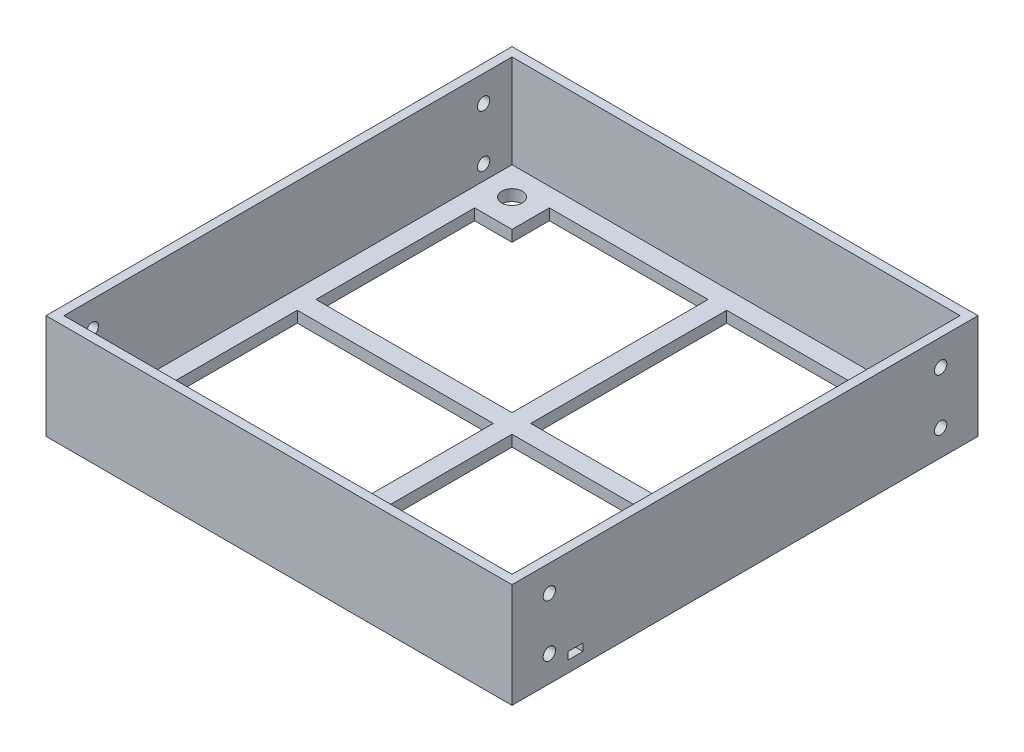
SolidWorks part; units mm, degrees
ref_plane "Front Plane" through (0, 0, 0) normal (0, 0, 1) x (1, 0, 0)
ref_plane "Top Plane" through (0, 0, 0) normal (0, 1, 0) x (1, 0, 0)
ref_plane "Right Plane" through (0, 0, 0) normal (1, 0, 0) x (0, 0, -1)
sketch "Sketch1" plane through (0, 0, 0) normal (0, 1, 0) x (1, 0, 0)
  line L9 (0, 0) -> (120, 0)
  line L10 (0, 0) -> (0, 120)
  line L11 (0, 120) -> (120, 120)
  line L12 (120, 0) -> (120, 120)
  dimension "D1" = 120
  dimension "D2" = 120
extrude "Boss-Extrude1" add sketch "Sketch1" along normal blind 3
sketch "Sketch2" plane through (0, 3, 0) normal (0, 1, 0) x (1, 0, 0)
  line L0 (0, 120) -> (120, 0) construction
  line L1 (0, 0) -> (120, 120) construction
  line L2 (0, 120) -> (0, 0) construction
  line L3 (15, 115) -> (57.5, 115)
  line L4 (5, 105) -> (5, 62.5)
  line L5 (5, 62.5) -> (57.5, 62.5)
  line L6 (57.5, 115) -> (57.5, 62.5)
  line L7 (60, 120) -> (60, 0) construction
  line L8 (120, 120) -> (0, 120) construction
  line L9 (0, 0) -> (120, 0) construction
  line L10 (62.5, 5) -> (62.5, 57.5)
  line L11 (115, 57.5) -> (62.5, 57.5)
  line L12 (115, 15) -> (115, 57.5)
  line L13 (105, 5) -> (62.5, 5)
  line L14 (5, 105) -> (5, 62.5)
  line L15 (15, 115) -> (57.5, 115)
  line L16 (57.5, 115) -> (57.5, 62.5)
  line L17 (5, 62.5) -> (57.5, 62.5)
  line L18 (62.5, 5) -> (62.5, 57.5)
  line L19 (115, 57.5) -> (62.5, 57.5)
  line L20 (115, 15) -> (115, 57.5)
  line L21 (105, 5) -> (62.5, 5)
  line L22 (15, 5) -> (57.5, 5)
  line L23 (5, 15) -> (5, 57.5)
  line L24 (5, 57.5) -> (57.5, 57.5)
  line L25 (57.5, 5) -> (57.5, 57.5)
  line L26 (115, 62.5) -> (62.5, 62.5)
  line L27 (62.5, 115) -> (62.5, 62.5)
  line L28 (105, 115) -> (62.5, 115)
  line L29 (115, 105) -> (115, 62.5)
  line L30 (105, 5) -> (105, 15)
  line L33 (5, 105) -> (15, 105)
  line L34 (15, 115) -> (15, 105)
  line L35 (115, 15) -> (105, 15)
  line L39 (5, 15) -> (15, 15)
  line L40 (15, 5) -> (15, 15)
  line L42 (115, 105) -> (105, 105)
  line L43 (105, 115) -> (105, 105)
  dimension "D1" = 5
  dimension "D2" = 2.5
  dimension "D3" = 15
  dimension "D4" = 5
extrude "Cut-Extrude1" cut sketch "Sketch2" against normal up to next and the other way through all contours L6 L3 L4 L5 | L29 L28 L27 L26 | L13 L12 L11 L10 | L22 L25 L24 L23
sketch "Sketch3" plane through (0, 3, 0) normal (0, 1, 0) x (1, 0, 0)
  line L0 (0, 120) -> (120, 0) construction
  line L1 (0, 0) -> (120, 120) construction
  line L2 (120, 120) -> (0, 120) construction
  line L3 (60, 120) -> (60, 0) construction
  line L4 (0, 0) -> (120, 0) construction
  line L5 (0, 60) -> (120, 60) construction
  line L6 (0, 120) -> (0, 0) construction
  line L7 (120, 0) -> (120, 120) construction
  circle A0 centre (7.5, 112.5) radius 2.75
  circle A1 centre (112.5, 112.5) radius 2.75
  circle A2 centre (112.5, 7.5) radius 2.75
  circle A3 centre (7.5, 7.5) radius 2.75
  dimension "D1" = 7.5
  dimension "D2" = 5.5
extrude "Cut-Extrude2" cut sketch "Sketch3" against normal up to next
sketch "Sketch5" plane through (0, 0, 0) normal (0, 1, 0) x (1, 0, 0)
  line L1 (0, 120) -> (120, 120)
  line L2 (0, 120) -> (0, 0)
  line L3 (0, 0) -> (120, 0)
  line L4 (120, 120) -> (120, 0)
  line L5 (-2.4, 122.4) -> (122.4, 122.4)
  line L6 (-2.4, 122.4) -> (-2.4, -2.4)
  line L7 (-2.4, -2.4) -> (122.4, -2.4)
  line L8 (122.4, 122.4) -> (122.4, -2.4)
  dimension "D1" = 2.4
  dimension "D2" = 2.4
  dimension "D3" = 2.4
  dimension "D4" = 2.4
extrude "Boss-Extrude2" add sketch "Sketch5" along normal blind 28
sketch "Sketch6" plane through (-2.4, 0, 0) normal (-1, 0, 0) x (0, 0, 1)
  line L0 (-122.4, 14) -> (2.4, 14) construction
  line L1 (-122.4, 28) -> (-122.4, 0) construction
  line L2 (2.4, 28) -> (2.4, 0) construction
  line L3 (-60, 14) -> (-60, 28) construction
  line L4 (-122.4, 28) -> (2.4, 28) construction
  line L5 (-60, 21) -> (-122.4, 21) construction
  circle A0 centre (-112.4, 21) radius 1.65
  circle A1 centre (-112.4, 7) radius 1.65
  circle A2 centre (-7.6, 7) radius 1.65
  circle A3 centre (-7.6, 21) radius 1.65
  dimension "D1" = 10
  dimension "D2" = 3.3
extrude "Cut-Extrude3" cut sketch "Sketch6" against normal through all
sketch "Sketch7" plane through (-2.4, 0, 0) normal (-1, 0, 0) x (0, 0, 1)
  line L0 (-122.4, 0) -> (2.4, 0) construction
  line L1 (-12.6, 3) -> (-16.6, 3)
  line L2 (-12.6, 3) -> (-12.6, 5)
  line L3 (-12.6, 5) -> (-16.6, 5)
  line L4 (-16.6, 3) -> (-16.6, 5)
  line L5 (2.4, 28) -> (2.4, 0) construction
  dimension "D3" = 3
  dimension "D1" = 4
  dimension "D2" = 2
  dimension "D4" = 15
extrude "Cut-Extrude4" cut sketch "Sketch7" against normal through all
